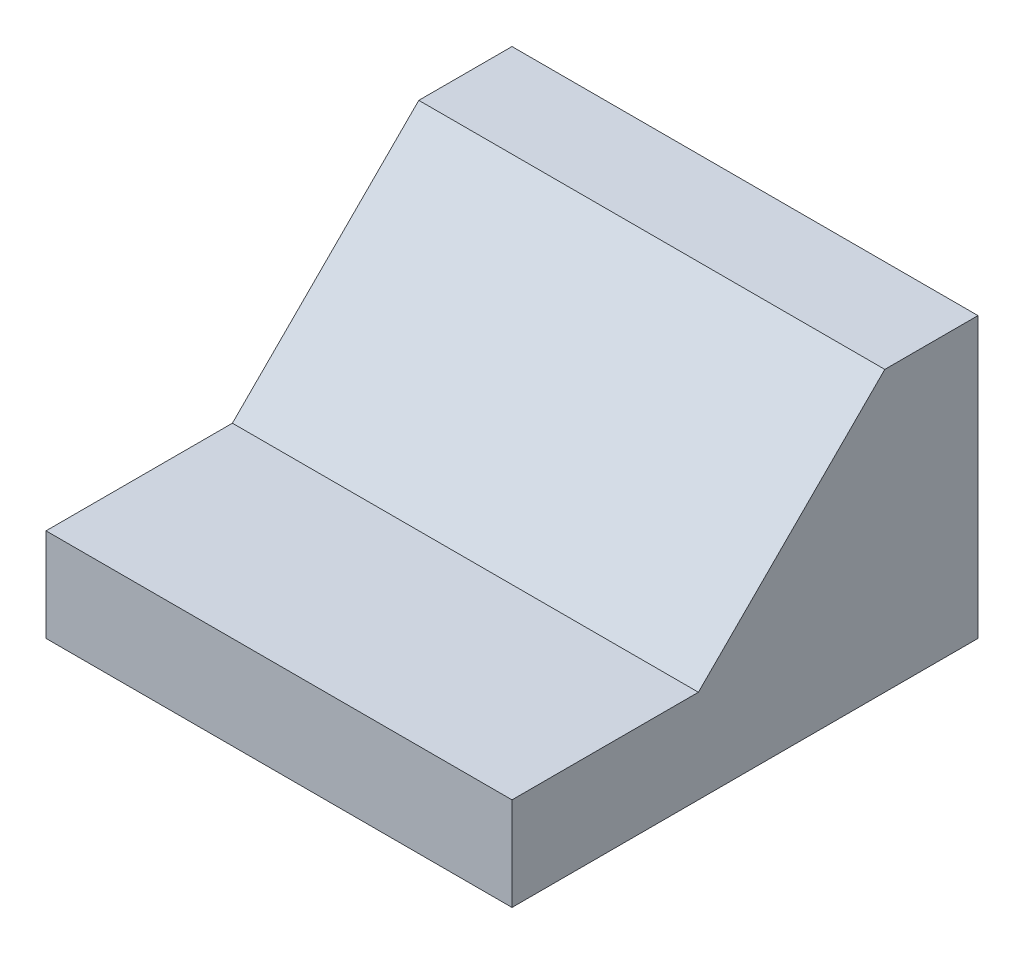
SolidWorks part; units mm, degrees
ref_plane "Front Plane" through (0, 0, 0) normal (0, 0, 1) x (1, 0, 0)
ref_plane "Top Plane" through (0, 0, 0) normal (0, 1, 0) x (1, 0, 0)
ref_plane "Right Plane" through (0, 0, 0) normal (1, 0, 0) x (0, 0, -1)
sketch "Sketch1" plane through (0, 0, 0) normal (1, 0, 0) x (0, 0, -1)
  line L0 (0, 0) -> (0, 6)
  line L1 (0, 6) -> (-2, 6)
  line L2 (-2, 6) -> (-6, 2)
  line L3 (-6, 2) -> (-10, 2)
  line L4 (-10, 2) -> (-10, 0)
  line L5 (-10, 0) -> (0, 0)
  line L6 (-2, 6) -> (-2, -18.525) construction
  dimension "D1" = 45
  dimension "D2" = 2
  dimension "D3" = 6
  dimension "D4" = 2
  dimension "D5" = 10
extrude "Boss-Extrude1" add sketch "Sketch1" along normal blind 10
